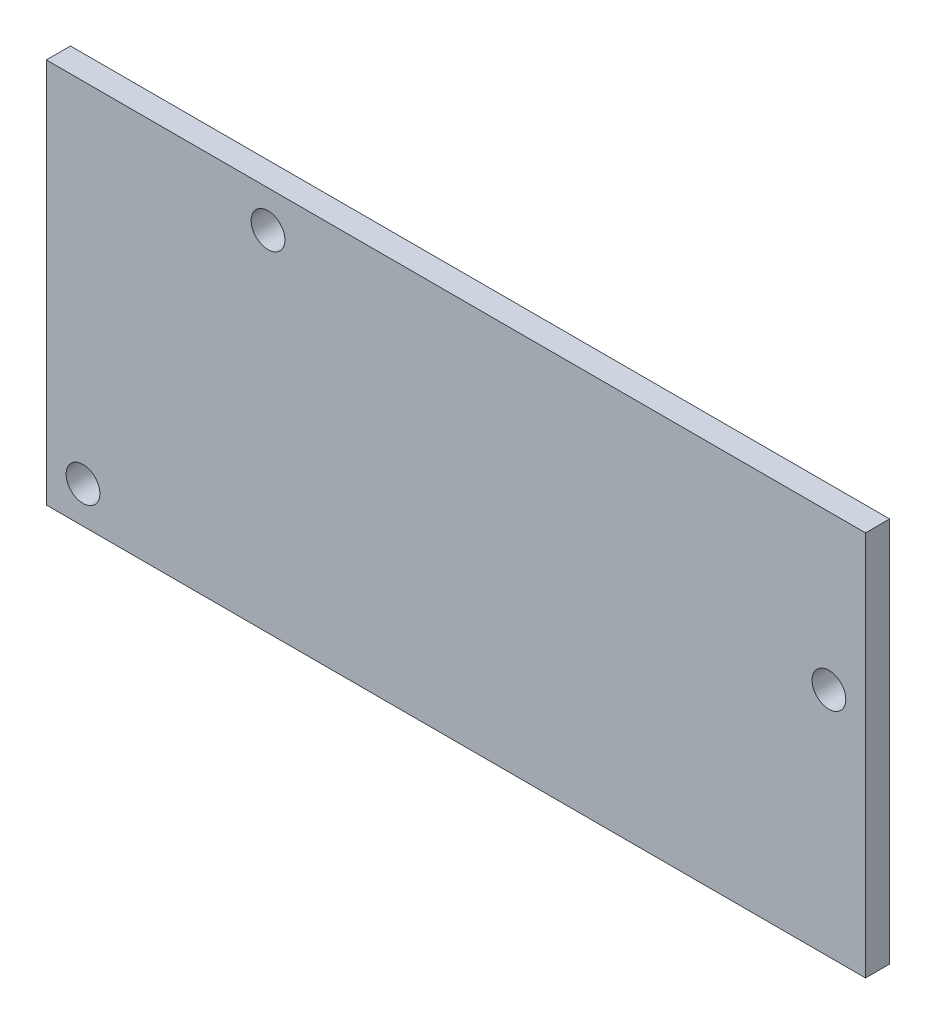
SolidWorks part; units mm, degrees
ref_plane "Plan de face" through (0, 0, 0) normal (0, 0, 1) x (1, 0, 0)
ref_plane "Plan de dessus" through (0, 0, 0) normal (0, 1, 0) x (1, 0, 0)
ref_plane "Plan de droite" through (0, 0, 0) normal (1, 0, 0) x (0, 0, -1)
sketch "Esquisse1" plane through (0, 0, 0) normal (0, 0, 1) x (1, 0, 0)
  line L1 (0, 0) -> (85, 0)
  line L2 (0, 0) -> (0, 40)
  line L3 (0, 40) -> (85, 40)
  line L4 (85, 0) -> (85, 40)
  circle A0 centre (23, 36.2) radius 1.75
  circle A1 centre (3.8, 3.8) radius 1.75
  circle A2 centre (81.2, 24) radius 1.75
  dimension "D3" = 3.5
  dimension "D1" = 40
  dimension "D2" = 85
  dimension "D4" = 23
  dimension "D5" = 3.8
  dimension "D6" = 3.8
  dimension "D7" = 3.8
  dimension "D8" = 16
  dimension "D9" = 3.8
extrude "Boss.-Extru.1" add sketch "Esquisse1" along normal blind 2.5
sketch "Esquisse2" plane through (0, 0, 0) normal (0, 0, -1) x (-1, 0, 0)
  line L1 (-58, 28.5) -> (-55, 28.5)
  line L2 (-58, 28.5) -> (-58, 11.5)
  line L3 (-58, 11.5) -> (-55, 11.5)
  line L4 (-55, 28.5) -> (-55, 11.5)
  line L5 (-85, 0) -> (-85, 40) construction
  line L6 (-118.624, 20) -> (20.6391, 20) construction
  line L7 (-85, 40) -> (0, 40) construction
  line L8 (0, 0) -> (-85, 0) construction
  dimension "D1" = 30
  dimension "D2" = 3
  dimension "D3" = 17
extrude "Boss.-Extru.2" add sketch "Esquisse2" along normal blind 12
sketch "Esquisse3" plane through (58, 0, 0) normal (1, 0, 0) x (0, 0, -1)
  line L0 (8.5, 32.2827) -> (8.5, 8.5025) construction
  line L1 (12, 28.5) -> (12, 11.5) construction
  line L2 (12, 28.5) -> (0, 28.5) construction
  line L3 (12, 11.5) -> (0, 11.5) construction
  circle A0 centre (8.5, 24.25) radius 1.75
  circle A1 centre (8.5, 15.75) radius 1.75
  dimension "D2" = 3.5
  dimension "D1" = 3.5
  dimension "D3" = 2.5
  dimension "D4" = 2.5
extrude "Enlèv. mat.-Extru.1" cut sketch "Esquisse3" against normal through all
fillet "Congé1" radius 2.5 4 edges at (56.5, 11.5, 0) (56.5, 11.5, -12) (56.5, 28.5, -12) (56.5, 28.5, 0)
